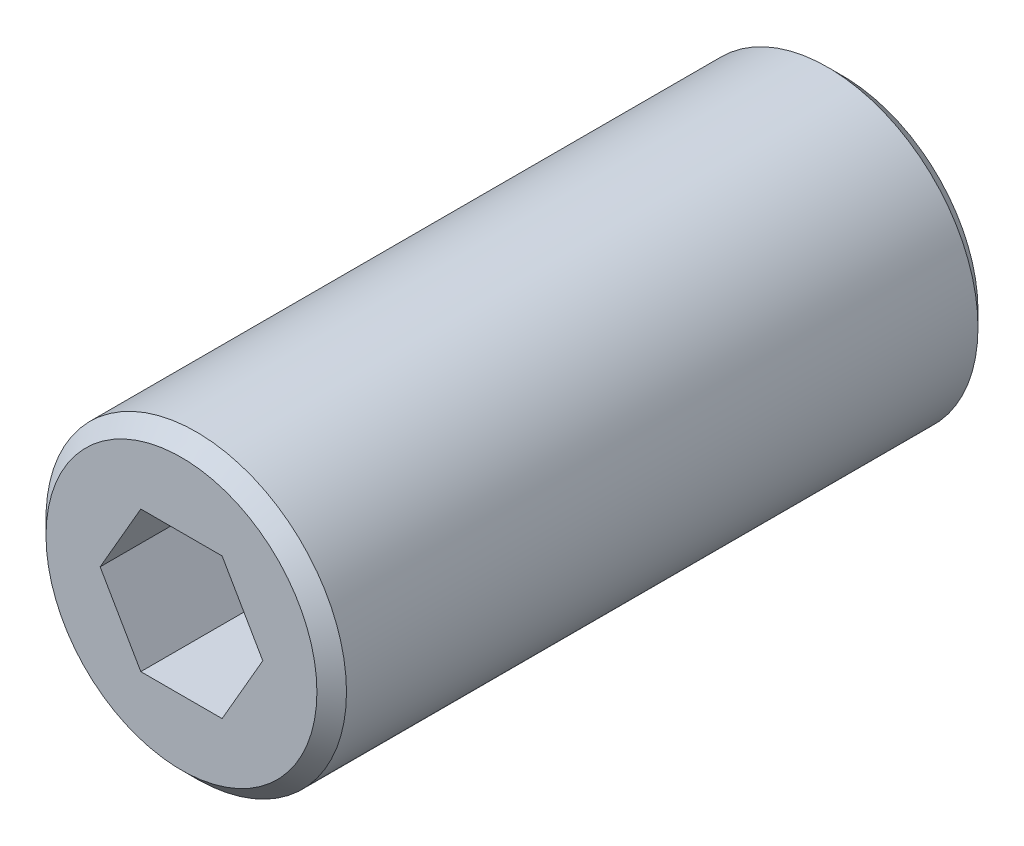
SolidWorks part; units mm, degrees
ref_plane "Front Plane" through (0, 0, 0) normal (0, 0, 1) x (1, 0, 0)
ref_plane "Top Plane" through (0, 0, 0) normal (0, 1, 0) x (1, 0, 0)
ref_plane "Right Plane" through (0, 0, 0) normal (1, 0, 0) x (0, 0, -1)
sketch "Sketch1" plane through (0, 0, 0) normal (0, 0, 1) x (1, 0, 0)
  line L1 (5.4993, 0) -> (2.7496, 4.7625)
  line L2 (2.7496, 4.7625) -> (-2.7496, 4.7625)
  line L3 (-2.7496, 4.7625) -> (-5.4993, 0)
  line L4 (-5.4993, 0) -> (-2.7496, -4.7625)
  line L5 (-2.7496, -4.7625) -> (2.7496, -4.7625)
  line L6 (2.7496, -4.7625) -> (5.4993, 0)
  circle A0 centre (0, 0) radius 10.16
  circle A1 centre (0, 0) radius 4.7625 construction
  dimension "D1" = 20.32
extrude "Boss-Extrude1" add sketch "Sketch1" along normal blind 44.704
chamfer "Chamfer1" distance 1 angle 45 2 edges at (10.16, 0, 0) (10.16, 0, 44.704)
